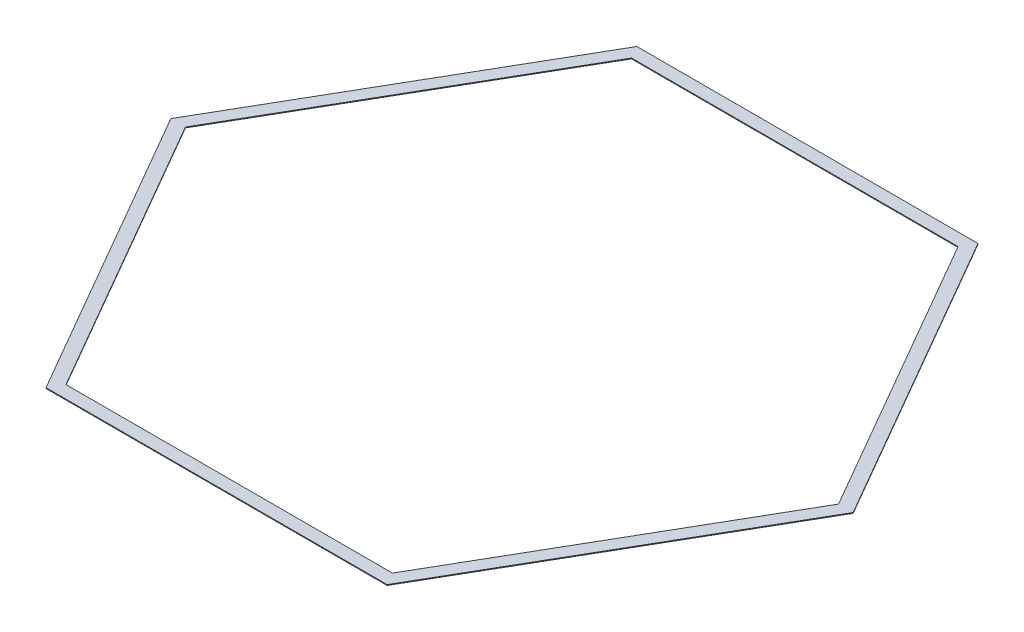
SolidWorks part; units mm, degrees
ref_plane "Front Plane" through (0, 0, 0) normal (0, 0, 1) x (1, 0, 0)
ref_plane "Top Plane" through (0, 0, 0) normal (0, 1, 0) x (1, 0, 0)
ref_plane "Right Plane" through (0, 0, 0) normal (1, 0, 0) x (0, 0, -1)
sketch "Sketch1" plane through (0, 0, 0) normal (0, 1, 0) x (1, 0, 0)
  line L0 (-685.5093, 1187.337) -> (-1371.0186, 0)
  line L1 (1312.3599, 0) -> (656.1799, 1136.537)
  line L2 (656.1799, 1136.537) -> (-656.1799, 1136.537)
  line L3 (-656.1799, 1136.537) -> (-1312.3599, 0)
  line L4 (-1312.3599, 0) -> (-656.1799, -1136.537)
  line L5 (-656.1799, -1136.537) -> (656.1799, -1136.537)
  line L6 (656.1799, -1136.537) -> (1312.3599, 0)
  line L7 (-1371.0186, 0) -> (-685.5093, -1187.337)
  line L8 (-685.5093, -1187.337) -> (685.5093, -1187.337)
  line L9 (685.5093, -1187.337) -> (1371.0186, 0)
  line L10 (1371.0186, 0) -> (685.5093, 1187.337)
  line L11 (685.5093, 1187.337) -> (-685.5093, 1187.337)
  circle A0 centre (0, 0) radius 1136.537 construction
  dimension "D2" = 2273.0739
  dimension "D1" = 50.8
extrude "Boss-Extrude1" add sketch "Sketch1" along normal blind 3.175
